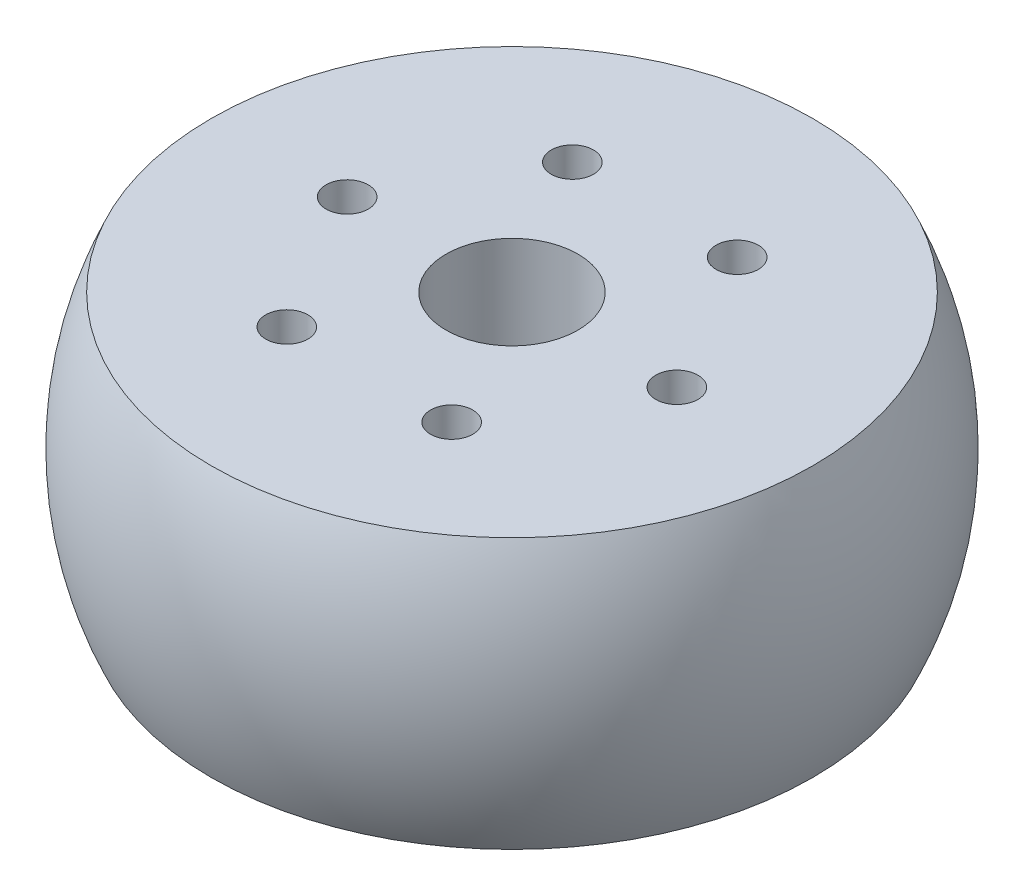
SolidWorks part; units mm, degrees
ref_plane "Front Plane" through (0, 0, 0) normal (0, 0, 1) x (1, 0, 0)
ref_plane "Top Plane" through (0, 0, 0) normal (0, 1, 0) x (1, 0, 0)
ref_plane "Right Plane" through (0, 0, 0) normal (1, 0, 0) x (0, 0, -1)
sketch "Sketch1" plane through (0, 0, 0) normal (1, 0, 0) x (0, 0, -1)
  line L0 (0, -6.5) -> (0, 6.5) construction
  line L1 (3.175, 6.5) -> (14.4833, 6.5)
  line L2 (3.175, 6.5) -> (3.175, -6.5)
  line L3 (3.175, -6.5) -> (14.4833, -6.5)
  line L4 (15.875, 0) -> (0, 0) construction
  circle A0 centre (0, 0) radius 15.875 construction
  arc A1 (14.4833, 6.5) -> (14.4833, -6.5) centre (0, 0) cw
  point P4 (0, 0)
  dimension "D1" = 6.35
  dimension "D2" = 13
  dimension "D3" = 15.875
revolve "Revolve1" add sketch "Sketch1" angle 360 about L0
sketch "Sketch3" plane through (0, 0, 0) normal (0, 1, 0) x (1, 0, 0)
  line L0 (0, 0) -> (7.9375, 0) construction
  circle A0 centre (7.9375, 0) radius 1.016
  dimension "D1" = 2.032
  dimension "D2" = 7.9375
extrude "Cut-Extrude1" cut sketch "Sketch3" against normal through all both and the other way through all
pattern_circular "CirPattern1" count 6 over 360 about axis through (0, 0, 0) along (0, 1, 0) of "Cut-Extrude1"
